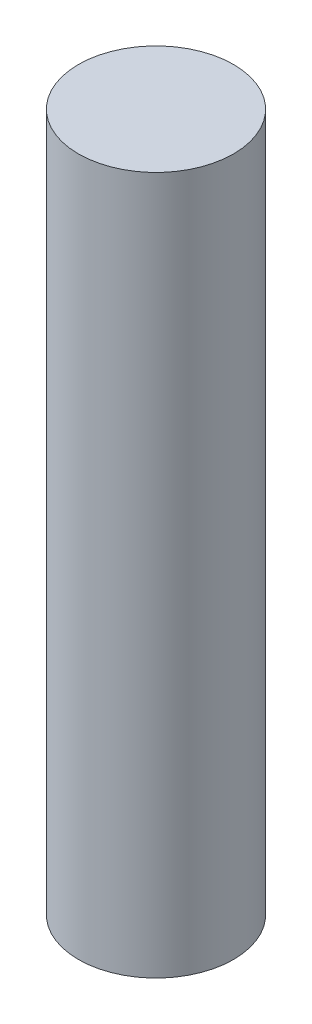
SolidWorks part; units mm, degrees
ref_plane "Front Plane" through (0, 0, 0) normal (0, 0, 1) x (1, 0, 0)
ref_plane "Top Plane" through (0, 0, 0) normal (0, 1, 0) x (1, 0, 0)
ref_plane "Right Plane" through (0, 0, 0) normal (1, 0, 0) x (0, 0, -1)
sketch "Sketch1" plane through (0, 0, 0) normal (0, 1, 0) x (1, 0, 0)
  circle A0 centre (0, 0) radius 12.7
  dimension "D1" = 25.4
extrude "Boss-Extrude1" add sketch "Sketch1" along normal blind 114.3
